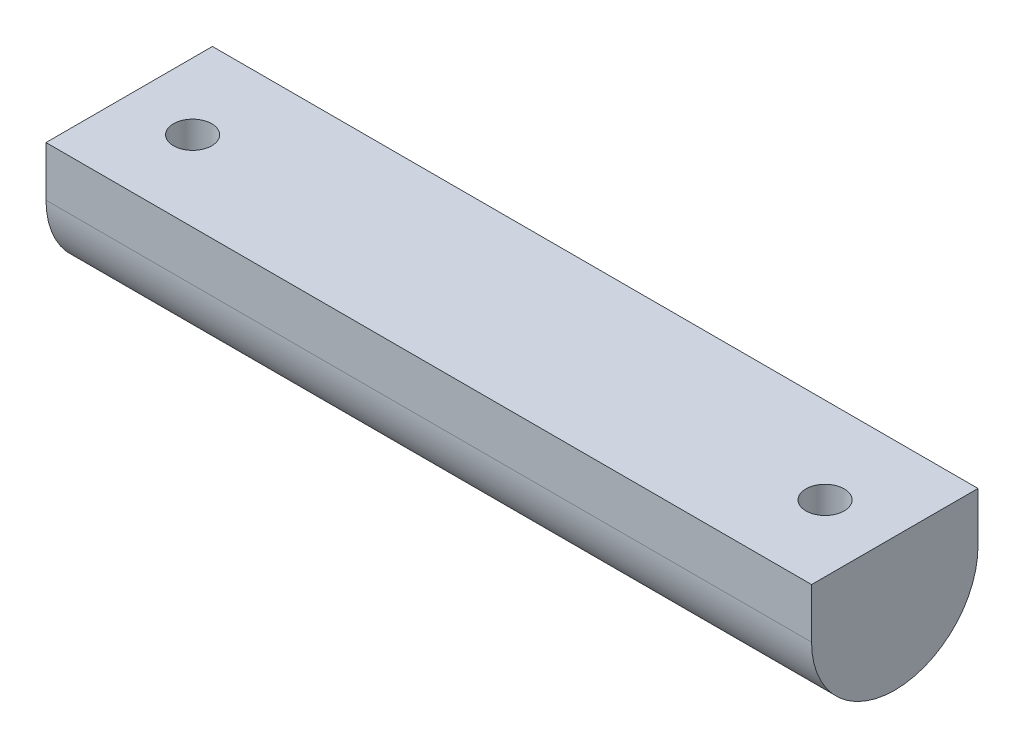
SolidWorks part; units mm, degrees
ref_plane "Front Plane" through (0, 0, 0) normal (0, 0, 1) x (1, 0, 0)
ref_plane "Top Plane" through (0, 0, 0) normal (0, 1, 0) x (1, 0, 0)
ref_plane "Right Plane" through (0, 0, 0) normal (1, 0, 0) x (0, 0, -1)
sketch "Sketch1" plane through (0, 0, 0) normal (1, 0, 0) x (0, 0, -1)
  line L1 (-24.0469, 0) -> (-24.0469, 15)
  line L2 (-24.0469, 15) -> (25.9531, 15)
  line L3 (25.9531, 15) -> (25.9531, 0)
  arc A0 (-24.0469, 0) -> (25.9531, 0) centre (0.9531, 0) ccw
  dimension "D1" = 50
  dimension "D2" = 15
extrude "Boss-Extrude1" add sketch "Sketch1" along normal blind 230
hole_wizard "Ø11.5 (11.5) Diameter Hole2" positions "Sketch6" profile "Sketch7" hole size "Ø11.5" standard "ANSI Metric" end condition through all
sketch "Sketch6" plane through (0, 15, 0) normal (0, 1, 0) x (1, 0, 0)
  point P0 (20, 0)
  point P2 (210, 0)
  dimension "D1" = 190
  dimension "D2" = 20
sketch "Sketch7" plane through (20, 15, 0) normal (1, 0, 0) x (0, 0, 1)
  line L0 (0, 0) -> (0, 40)
  line L1 (0, 40) -> (5.75, 40)
  line L2 (5.75, 40) -> (5.75, 0)
  line L5 (5.75, 0) -> (0, 0)
  line L11 (0, -6.35) -> (0, 107.95) construction
  dimension "Thru Hole Dia." = 11.5
  dimension "Thru Hole Depth" = 40
